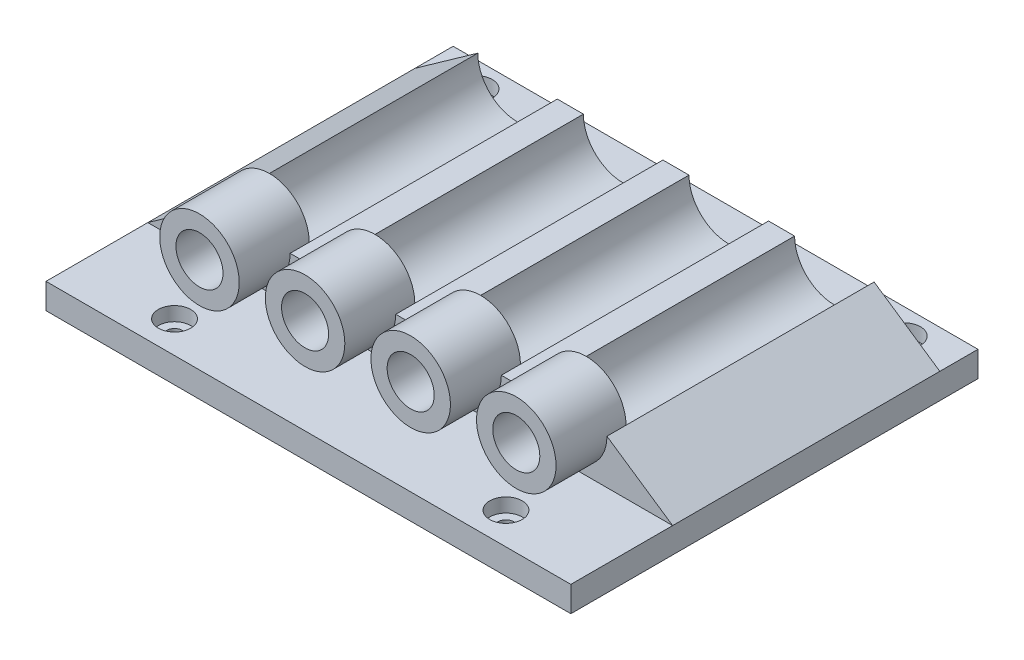
SolidWorks part; units mm, degrees
ref_plane "Front Plane" through (0, 0, 0) normal (0, 0, 1) x (1, 0, 0)
ref_plane "Top Plane" through (0, 0, 0) normal (0, 1, 0) x (1, 0, 0)
ref_plane "Right Plane" through (0, 0, 0) normal (1, 0, 0) x (0, 0, -1)
sketch "Sketch1" plane through (0, 0, 0) normal (0, 1, 0) x (1, 0, 0)
  line L1 (-52.3875, -40.64) -> (52.3875, -40.64)
  line L2 (-52.3875, -40.64) -> (-52.3875, 40.64)
  line L3 (-52.3875, 40.64) -> (52.3875, 40.64)
  line L4 (52.3875, -40.64) -> (52.3875, 40.64)
  line L5 (-52.3875, -40.64) -> (52.3875, 40.64) construction
  line L6 (-52.3875, 40.64) -> (52.3875, -40.64) construction
  point P0 (0, 0)
  dimension "D1" = 104.775
  dimension "D2" = 81.28
extrude "Boss-Extrude1" add sketch "Sketch1" along normal mid plane 5.08
sketch "Sketch2" plane through (0, 2.54, 0) normal (0, 1, 0) x (1, 0, 0)
  line L0 (0, 52.7353) -> (0, -48.7137) construction
  line L1 (52.3875, -40.64) -> (52.3875, 40.64) construction
  line L2 (52.3875, 40.64) -> (-52.3875, 40.64) construction
  circle A0 centre (33.0835, -34.29) radius 1.5875
  circle A1 centre (42.7355, 35.56) radius 1.5875
  circle A2 centre (-33.0835, -34.29) radius 1.5875
  circle A3 centre (-42.7355, 35.56) radius 1.5875
  dimension "D5" = 3.175
  dimension "D1" = 9.652
  dimension "D2" = 9.652
  dimension "D3" = 69.85
  dimension "D4" = 5.08
extrude "Cut-Extrude1" cut sketch "Sketch2" against normal up to next contours A2 | A0 | A1 | A3
sketch "Sketch7" plane through (0, 0, 0) normal (0, 0, 1) x (1, 0, 0)
  line L0 (-23.9741, 11.43) -> (-18.7671, 11.43)
  line L1 (18.1899, 11.43) -> (23.3969, 11.43)
  line L2 (-2.8921, 11.43) -> (2.3149, 11.43)
  line L3 (-52.3875, 2.54) -> (52.3875, 2.54) construction
  line L4 (-52.3875, 2.54) -> (52.3875, 2.54)
  line L5 (39.2719, 11.43) -> (52.3875, 2.54)
  line L6 (-39.8491, 11.43) -> (-52.3875, 2.54)
  arc A0 (-39.8491, 11.43) -> (-23.9741, 11.43) centre (-31.9116, 11.43) ccw
  arc A2 (-18.7671, 11.43) -> (-2.8921, 11.43) centre (-10.8296, 11.43) ccw
  arc A3 (2.3149, 11.43) -> (18.1899, 11.43) centre (10.2524, 11.43) ccw
  arc A4 (23.3969, 11.43) -> (39.2719, 11.43) centre (31.3344, 11.43) ccw
  point P14 (0, 0)
  point P15 (0, 0)
  dimension "D2" = 15.875
  dimension "D3" = 21.082
  dimension "D4" = 8.89
  dimension "D1" = 4
extrude "Boss-Extrude7" add sketch "Sketch7" along normal blind 20.32 and the other way blind 33.02 contours A2 L2 A3 L1 A4 L5 L4 L6 A0 L0
sketch "Sketch8" plane through (0, 0, 20.32) normal (0, 0, 1) x (1, 0, 0)
  circle A0 centre (-31.9116, 11.43) radius 7.9375
  circle A1 centre (-10.8296, 11.43) radius 7.9375
  circle A2 centre (10.2524, 11.43) radius 7.9375
  circle A3 centre (31.3344, 11.43) radius 7.9375
  arc A4 (-39.8491, 11.43) -> (-23.9741, 11.43) centre (-31.9116, 11.43) ccw construction
extrude "Boss-Extrude8" add sketch "Sketch8" along normal blind 10.16 and the other way blind 3.81 separate body
sketch "Sketch11" plane through (0, 2.54, 0) normal (0, 1, 0) x (1, 0, 0)
  circle A0 centre (-42.7355, 35.56) radius 1.5875 construction
  circle A1 centre (42.7355, 35.56) radius 1.5875 construction
  circle A2 centre (33.0835, -34.29) radius 1.5875 construction
  circle A3 centre (-42.7355, 35.56) radius 1.5875 construction
  circle A4 centre (42.7355, 35.56) radius 1.5875 construction
  circle A5 centre (33.0835, -34.29) radius 1.5875 construction
  circle A6 centre (-33.0835, -34.29) radius 1.5875 construction
  circle A7 centre (-33.0835, -34.29) radius 1.5875 construction
  circle A8 centre (-33.0835, -34.29) radius 3.2385
  circle A9 centre (33.0835, -34.29) radius 3.2385
  circle A10 centre (42.7355, 35.56) radius 3.2385
  circle A11 centre (-42.7355, 35.56) radius 3.2385
  dimension "D1" = 1.651
extrude "Cut-Extrude4" cut sketch "Sketch11" against normal blind 2.794
sketch "Sketch9" plane through (0, 0, 16.51) normal (0, 0, -1) x (-1, 0, 0)
  circle A0 centre (-31.3344, 11.43) radius 1.27
  circle A1 centre (-10.2524, 11.43) radius 1.27
  circle A2 centre (10.8296, 11.43) radius 1.27
  circle A3 centre (31.9116, 11.43) radius 1.27
  circle A4 centre (-10.2524, 11.43) radius 7.9375 construction
  dimension "D1" = 2.54
extrude "Cut-Extrude2" cut sketch "Sketch9" against normal up to next (13.97 mm away)
sketch "Sketch10" plane through (0, 0, 30.48) normal (0, 0, 1) x (1, 0, 0)
  circle A0 centre (31.3344, 11.43) radius 1.27 construction
  circle A1 centre (10.2524, 11.43) radius 1.27 construction
  circle A2 centre (-10.8296, 11.43) radius 1.27 construction
  circle A3 centre (-31.9116, 11.43) radius 1.27 construction
  circle A4 centre (31.3344, 11.43) radius 1.27
  circle A5 centre (10.2524, 11.43) radius 1.27
  circle A6 centre (-10.8296, 11.43) radius 1.27
  circle A7 centre (-31.9116, 11.43) radius 1.27
  circle A8 centre (-31.9116, 11.43) radius 4.699
  circle A9 centre (-10.8296, 11.43) radius 4.699
  circle A10 centre (10.2524, 11.43) radius 4.699
  circle A11 centre (31.3344, 11.43) radius 4.699
  dimension "D1" = 3.429
  dimension "D2" = 3.429
extrude "Cut-Extrude3" cut sketch "Sketch10" against normal blind 10.795
